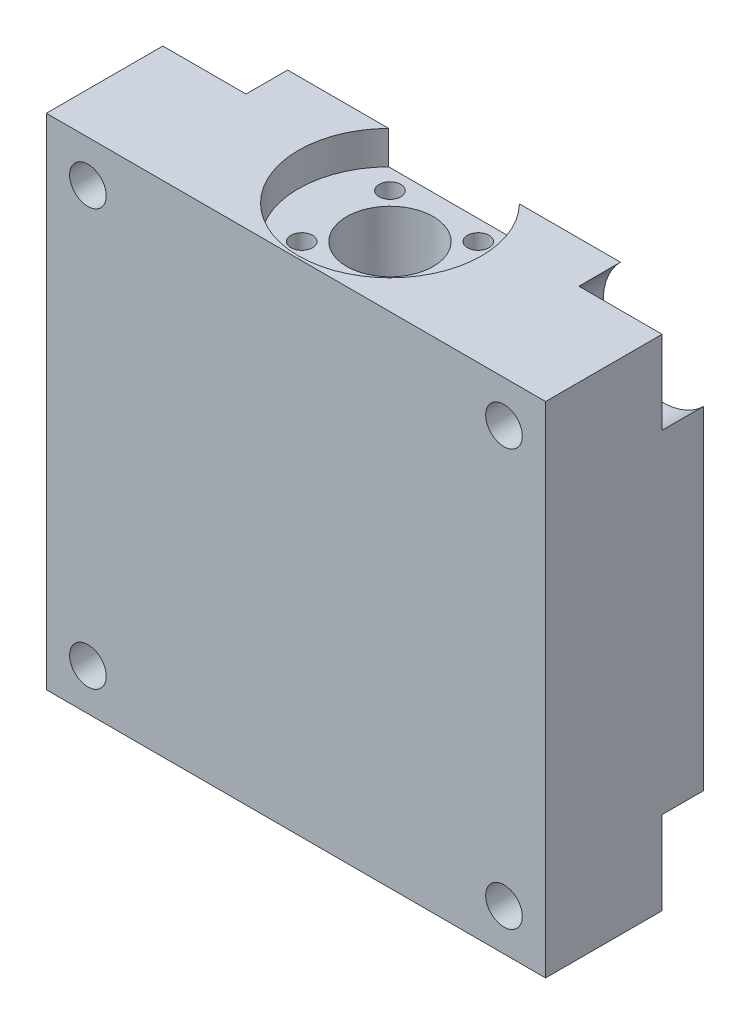
SolidWorks part; units mm, degrees
ref_plane "Front Plane" through (0, 0, 0) normal (0, 0, 1) x (1, 0, 0)
ref_plane "Top Plane" through (0, 0, 0) normal (0, 1, 0) x (1, 0, 0)
ref_plane "Right Plane" through (0, 0, 0) normal (1, 0, 0) x (0, 0, -1)
sketch "Sketch1" plane through (0, 0, 0) normal (0, 0, 1) x (1, 0, 0)
  line L1 (-30, 30) -> (30, 30)
  line L2 (-30, 30) -> (-30, -30)
  line L3 (-30, -30) -> (30, -30)
  line L4 (30, 30) -> (30, -30)
  line L5 (-30, 30) -> (30, -30) construction
  line L6 (-30, -30) -> (30, 30) construction
  line L7 (-25, -25) -> (25, -25) construction
  line L8 (-25, -25) -> (-25, 25) construction
  line L9 (-25, 25) -> (25, 25) construction
  line L10 (25, -25) -> (25, 25) construction
  line L11 (-25, -25) -> (25, 25) construction
  line L12 (-25, 25) -> (25, -25) construction
  circle A0 centre (-25, 25) radius 2.2
  circle A1 centre (25, 25) radius 2.2
  circle A2 centre (25, -25) radius 2.2
  circle A3 centre (-25, -25) radius 2.2
  point P0 (0, 0)
  point P6 (0, 0)
  dimension "D1" = 60
  dimension "D2" = 60
  dimension "D3" = 50
  dimension "D4" = 50
extrude "Boss-Extrude1" add sketch "Sketch1" along normal blind 19
sketch "Sketch2" plane through (0, 30, 0) normal (0, 1, 0) x (1, 0, 0)
  line L0 (30, 0) -> (-30, 0) construction
  circle A0 centre (0, -7.7) radius 11
  dimension "D1" = 7.7
extrude "Cut-Extrude1" cut sketch "Sketch2" against normal blind 4
sketch "Sketch3" plane through (0, 26, 0) normal (0, 1, 0) x (1, 0, 0)
  circle A0 centre (0, -7.7) radius 5.2
extrude "Cut-Extrude2" cut sketch "Sketch3" against normal up to next
sketch "Sketch4" plane through (0, -30, 0) normal (0, -1, 0) x (1, 0, 0)
  circle A0 centre (0, 7.7) radius 7.2
extrude "Cut-Extrude3" cut sketch "Sketch4" against normal blind 46
sketch "Sketch5" plane through (0, 26, 0) normal (0, 1, 0) x (1, 0, 0)
  circle B0 centre (0, -7.7) radius 7.5 construction
  circle B1 centre (-5.3033, -2.3967) radius 1.3
  circle B2 centre (5.3033, -2.3967) radius 1.3
  circle B3 centre (5.3033, -13.0033) radius 1.3
  circle B4 centre (-5.3033, -13.0033) radius 1.3
sketch_block_instance "Block1-1"
sketch_block "Block1"
extrude "Cut-Extrude4" cut sketch "Sketch5" against normal blind 6
sketch "Sketch6" plane through (0, 0, 0) normal (0, 0, -1) x (-1, 0, 0)
  circle A0 centre (-25, 25) radius 7.0711
  circle A1 centre (25, 25) radius 7.0711
  circle A2 centre (25, -25) radius 7.0711
  circle A3 centre (-25, -25) radius 7.0711
extrude "Cut-Extrude5" cut sketch "Sketch6" against normal blind 5
